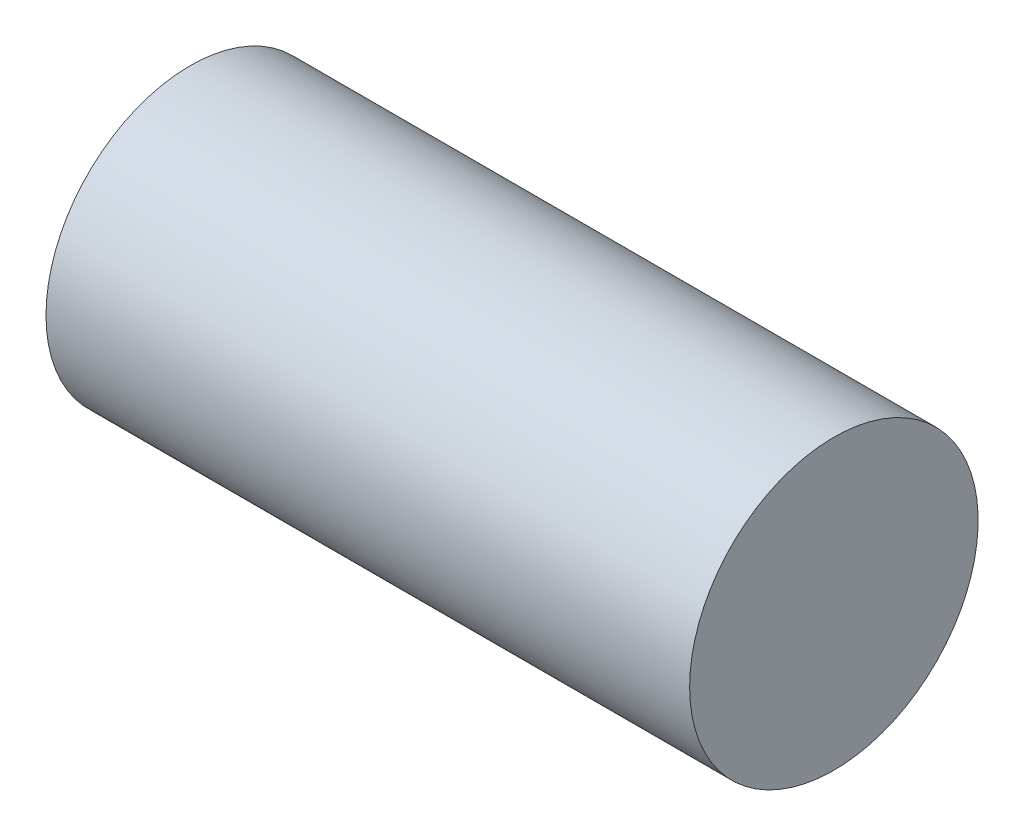
SolidWorks part; units mm, degrees
material "Water"
ref_plane "Front Plane" through (0, 0, 0) normal (0, 0, 1) x (1, 0, 0)
ref_plane "Top Plane" through (0, 0, 0) normal (0, 1, 0) x (1, 0, 0)
ref_plane "Right Plane" through (0, 0, 0) normal (1, 0, 0) x (0, 0, -1)
sketch "Sketch1" plane through (0, 0, 0) normal (0, 1, 0) x (1, 0, 0)
  line L1 (0, 0) -> (58, 0)
  line L2 (0, 0) -> (0, 13)
  line L3 (0, 13) -> (58, 13)
  line L4 (58, 0) -> (58, 13)
  dimension "D1" = 13
  dimension "D2" = 58
revolve "Revolve1" add sketch "Sketch1" angle 360 about L3
